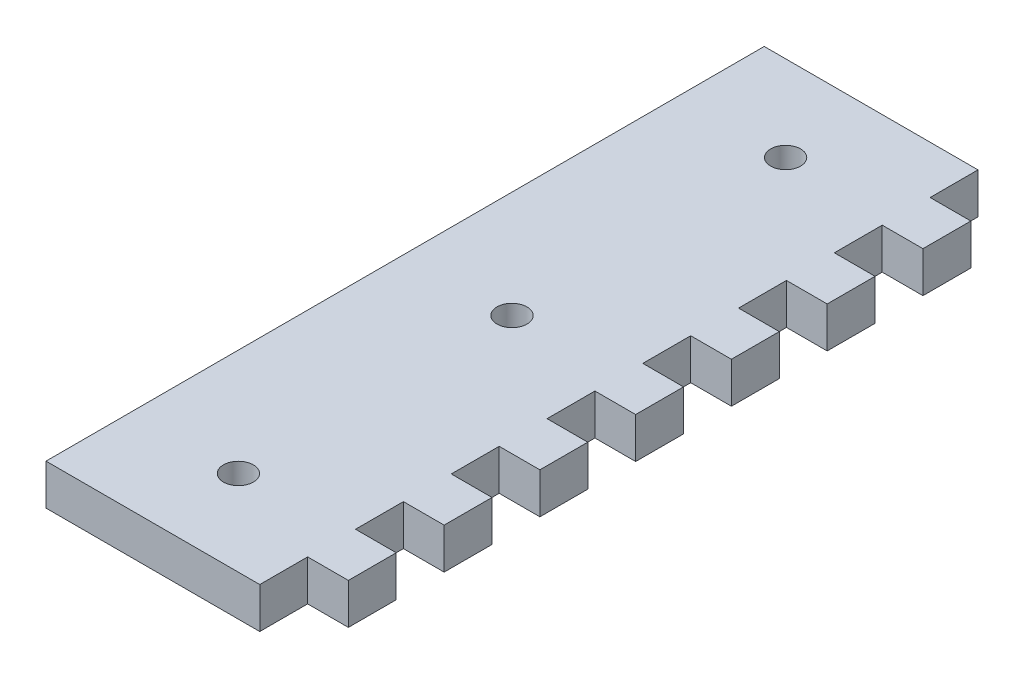
SolidWorks part; units mm, degrees
ref_plane "Front Plane" through (0, 0, 0) normal (0, 0, 1) x (1, 0, 0)
ref_plane "Top Plane" through (0, 0, 0) normal (0, 1, 0) x (1, 0, 0)
ref_plane "Right Plane" through (0, 0, 0) normal (1, 0, 0) x (0, 0, -1)
sketch "Sketch1" plane through (0, 0, 0) normal (0, 1, 0) x (1, 0, 0)
  line L0 (12.5, 84) -> (12.5, 0) construction
  line L1 (0, 0) -> (25, 0)
  line L2 (0, 0) -> (0, 84)
  line L3 (0, 84) -> (25, 84)
  line L4 (25, 0) -> (25, 84)
  line L5 (25, 0) -> (25, 5.6) construction
  line L6 (25, 5.6) -> (29.7625, 5.6)
  line L7 (29.7625, 5.6) -> (29.7625, 11.2)
  line L8 (29.7625, 11.2) -> (25, 11.2)
  line L9 (25, 84) -> (25, 78.4) construction
  line L10 (29.7625, 22.4) -> (25, 22.4)
  line L11 (29.7625, 16.8) -> (29.7625, 22.4)
  line L12 (25, 16.8) -> (29.7625, 16.8)
  line L13 (29.7625, 33.6) -> (25, 33.6)
  line L14 (29.7625, 28) -> (29.7625, 33.6)
  line L15 (25, 28) -> (29.7625, 28)
  line L16 (29.7625, 44.8) -> (25, 44.8)
  line L17 (29.7625, 39.2) -> (29.7625, 44.8)
  line L18 (25, 39.2) -> (29.7625, 39.2)
  line L19 (29.7625, 56) -> (25, 56)
  line L20 (29.7625, 50.4) -> (29.7625, 56)
  line L21 (25, 50.4) -> (29.7625, 50.4)
  line L22 (29.7625, 67.2) -> (25, 67.2)
  line L23 (29.7625, 61.6) -> (29.7625, 67.2)
  line L24 (25, 61.6) -> (29.7625, 61.6)
  line L25 (29.7625, 78.4) -> (25, 78.4)
  line L26 (29.7625, 72.8) -> (29.7625, 78.4)
  line L27 (25, 72.8) -> (29.7625, 72.8)
  circle A0 centre (12.5, 74) radius 1.75
  circle A1 centre (12.5, 42) radius 1.75
  circle A2 centre (12.5, 10) radius 1.75
  point P11 (54.5231, 78.0907)
  point P15 (25, 42)
  point P20 (56.5543, 74.5272)
  point P44 (55.1701, 11.2)
  point P45 (53.9469, 67.2)
  dimension "D2" = 3.5
  dimension "D1" = 84
  dimension "D3" = 10
  dimension "D4" = 10
  dimension "D5" = 5.6
  dimension "D6" = 5.6
  dimension "D8" = 4.7625
  dimension "D9" = 5.6
  dimension "D10" = 25
  dimension "D7" = 7
extrude "Boss-Extrude1" add sketch "Sketch1" along normal blind 4.7625 contours L1 L4 L3 L2 A2 A1 A0 | L4 L15 L14 L13 | L4 L12 L11 L10 | L4 L18 L17 L16 | L4 L21 L20 L19 | L4 L24 L23 L22 | L4 L27 L26 L25 | L7 L8 L4 L6
